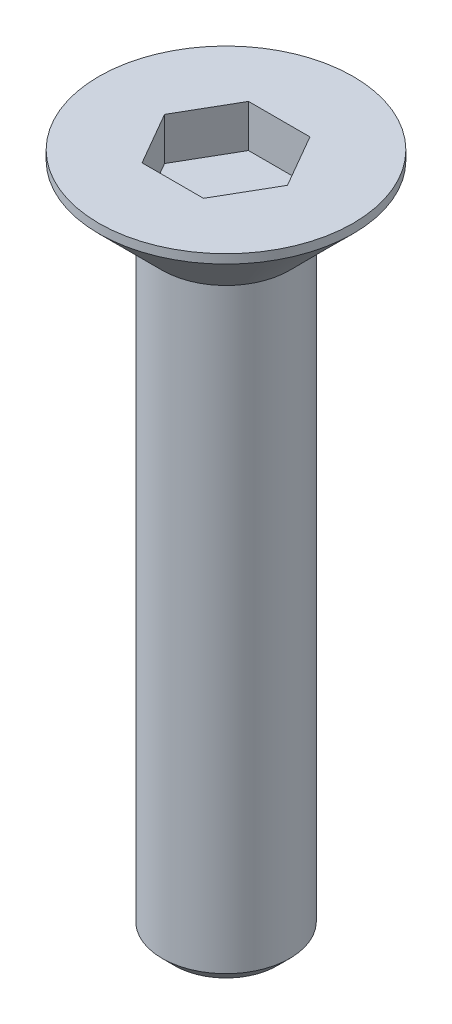
SolidWorks part; units mm, degrees
material "acero"
ref_plane "Alzado" through (0, 0, 0) normal (0, 0, 1) x (1, 0, 0)
ref_plane "Planta" through (0, 0, 0) normal (0, 1, 0) x (1, 0, 0)
ref_plane "Vista lateral" through (0, 0, 0) normal (1, 0, 0) x (0, 0, -1)
sketch "Croquis1" plane through (0, 0, 0) normal (0, 0, 1) x (1, 0, 0)
  line L0 (0, 0) -> (0, -60.9498) construction
  line L1 (0, 0) -> (3.2, 0)
  line L2 (1.5, -1.7) -> (3.2, 0)
  line L4 (1.5, -1.7) -> (1.5, -16)
  line L5 (1.5, -16) -> (0, -16)
  line L6 (0, -16) -> (0, 0)
  dimension "D1" = 16
  dimension "D2" = 45
  dimension "D3" = 1.7
  dimension "D4" = 3
revolve "Revolución1" add sketch "Croquis1" angle 360 about L0
chamfer "Chaflán2" distance 0.3 angle 45 1 edges at (0, 0, 3.2)
chamfer "Chaflán3" distance 0.3 angle 45 1 edges at (0, -16, 1.5)
sketch "Croquis3" plane through (0, 0, 0) normal (0, 1, 0) x (1, 0, 0)
  line L1 (-0.7217, 1.25) -> (-1.4434, 0)
  line L2 (-1.4434, 0) -> (-0.7217, -1.25)
  line L3 (-0.7217, -1.25) -> (0.7217, -1.25)
  line L4 (0.7217, -1.25) -> (1.4434, 0)
  line L5 (1.4434, 0) -> (0.7217, 1.25)
  line L6 (0.7217, 1.25) -> (-0.7217, 1.25)
  circle A0 centre (0, 0) radius 1.25 construction
  dimension "D1" = 2.5
extrude "Cortar-Extruir2" cut sketch "Croquis3" against normal blind 1
